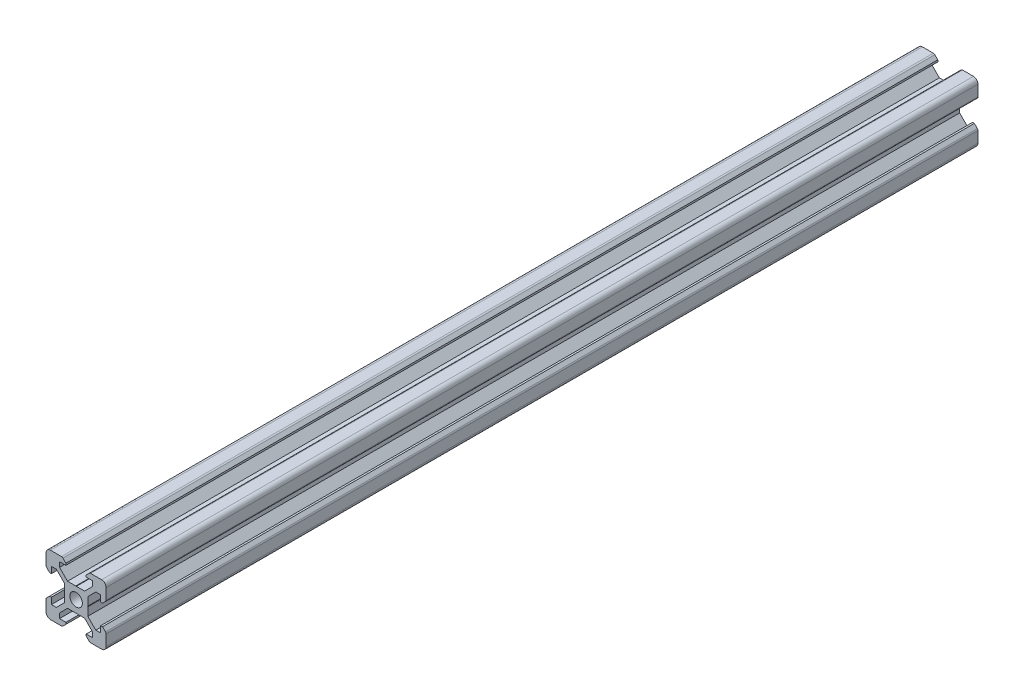
SolidWorks part; units mm, degrees
ref_plane "Front" through (0, 0, 0) normal (0, 0, 1) x (1, 0, 0)
ref_plane "Top" through (0, 0, 0) normal (0, 1, 0) x (1, 0, 0)
ref_plane "Right" through (0, 0, 0) normal (1, 0, 0) x (0, 0, -1)
sketch "Sketch1" plane through (0, 0, 0) normal (0, 0, 1) x (1, 0, 0)
  line L0 (-8.5, 10) -> (-10, 8.5) construction
  line L1 (-8.5, 10) -> (-4.8628, 10)
  line L2 (-10, 8.5) -> (-10, 4.8628)
  line L3 (-8.5, -10) -> (-4.8628, -10)
  line L4 (10, 8.5) -> (10, 4.8628)
  line L5 (-10, 10) -> (10, -10) construction
  line L6 (-10, -10) -> (10, 10) construction
  line L7 (-5.5, -8.2) -> (-3.3865, -8.2)
  line L8 (-8.2, -5.5) -> (-8.2, -3.3865)
  line L9 (-5.5, 8.2) -> (-3.3865, 8.2)
  line L10 (8.2, -5.5) -> (8.2, -3.3865)
  line L11 (-3.9005, 2.8395) -> (-6.561, 5.5)
  line L12 (-6.561, 5.5) -> (-8.2, 5.5)
  line L13 (-2.8395, -3.9005) -> (-0.1, -3.9005)
  line L14 (-3.9005, -2.8395) -> (-3.9005, -0.1)
  line L15 (-2.8395, 3.9005) -> (-0.1, 3.9005)
  line L16 (3.9005, -2.8395) -> (3.9005, -0.1)
  line L17 (-8.2, 3.3865) -> (-8.81, 3.3865)
  line L18 (-8.81, 3.3865) -> (-9.7976, 4.3741)
  line L19 (8.5, 10) -> (10, 8.5) construction
  line L20 (-2.8395, 3.9005) -> (-5.5, 6.561)
  line L21 (-5.5, 6.561) -> (-5.5, 8.2)
  line L22 (-3.3865, 8.2) -> (-3.3865, 8.81)
  line L23 (-3.3865, 8.81) -> (-4.3741, 9.7976)
  line L24 (0, 24.069) -> (0, -33.8154) construction
  line L25 (3.3865, 8.81) -> (4.3741, 9.7976)
  line L26 (3.3865, 8.2) -> (3.3865, 8.81)
  line L27 (5.5, 6.561) -> (5.5, 8.2)
  line L28 (2.8395, 3.9005) -> (5.5, 6.561)
  line L29 (3.3865, 8.2) -> (5.5, 8.2)
  line L30 (4.8628, 10) -> (8.5, 10)
  line L31 (-0.1, 3.9005) -> (0, 3.8005)
  line L32 (0.1, 3.9005) -> (0, 3.8005)
  line L33 (0.1, 3.9005) -> (2.8395, 3.9005)
  line L34 (25.9287, 0) -> (-28.3459, 0) construction
  line L35 (-0.1, -3.9005) -> (0, -3.8005)
  line L36 (0.1, -3.9005) -> (0, -3.8005)
  line L37 (0.1, -3.9005) -> (2.8395, -3.9005)
  line L38 (-3.9005, 0.1) -> (-3.8005, 0)
  line L39 (-3.8005, 0) -> (-3.9005, -0.1)
  line L40 (-3.9005, 0.1) -> (-3.9005, 2.8395)
  line L41 (3.9005, 0.1) -> (3.8005, 0)
  line L42 (3.8005, 0) -> (3.9005, -0.1)
  line L43 (3.9005, 0.1) -> (3.9005, 2.8395)
  line L44 (8.81, 3.3865) -> (9.7976, 4.3741)
  line L45 (8.2, 3.3865) -> (8.81, 3.3865)
  line L46 (6.561, 5.5) -> (8.2, 5.5)
  line L47 (3.9005, 2.8395) -> (6.561, 5.5)
  line L48 (2.8395, -3.9005) -> (5.5, -6.561)
  line L49 (3.9005, -2.8395) -> (6.561, -5.5)
  line L50 (-2.8395, -3.9005) -> (-5.5, -6.561)
  line L51 (-3.9005, -2.8395) -> (-6.561, -5.5)
  line L52 (6.561, -5.5) -> (8.2, -5.5)
  line L53 (-6.561, -5.5) -> (-8.2, -5.5)
  line L54 (-8.81, -3.3865) -> (-9.7976, -4.3741)
  line L55 (-8.2, -3.3865) -> (-8.81, -3.3865)
  line L56 (8.81, -3.3865) -> (9.7976, -4.3741)
  line L57 (8.2, -3.3865) -> (8.81, -3.3865)
  line L58 (8.2, 3.3865) -> (8.2, 5.5)
  line L59 (10, -4.8628) -> (10, -8.5)
  line L60 (-8.2, 3.3865) -> (-8.2, 5.5)
  line L61 (-10, -4.8628) -> (-10, -8.5)
  line L62 (-3.3865, -8.81) -> (-4.3741, -9.7976)
  line L63 (-3.3865, -8.2) -> (-3.3865, -8.81)
  line L64 (3.3865, -8.81) -> (4.3741, -9.7976)
  line L65 (3.3865, -8.2) -> (3.3865, -8.81)
  line L66 (-5.5, -6.561) -> (-5.5, -8.2)
  line L67 (5.5, -6.561) -> (5.5, -8.2)
  line L68 (3.3865, -8.2) -> (5.5, -8.2)
  line L69 (4.8628, -10) -> (8.5, -10)
  circle A0 centre (0, 0) radius 2.1
  arc A1 (-8.5, 10) -> (-10, 8.5) centre (-8.5, 8.5) ccw
  arc A2 (10, 8.5) -> (8.5, 10) centre (8.5, 8.5) ccw
  arc A3 (-4.3741, 9.7976) -> (-4.8628, 10) centre (-4.8628, 9.3088) ccw
  arc A4 (4.8628, 10) -> (4.3741, 9.7976) centre (4.8628, 9.3088) ccw
  arc A5 (-8.5, -10) -> (-10, -8.5) centre (-8.5, -8.5) cw
  arc A6 (9.7976, 4.3741) -> (10, 4.8628) centre (9.3088, 4.8628) ccw
  arc A7 (-10, 4.8628) -> (-9.7976, 4.3741) centre (-9.3088, 4.8628) ccw
  arc A8 (-10, -4.8628) -> (-9.7976, -4.3741) centre (-9.3088, -4.8628) cw
  arc A9 (9.7976, -4.3741) -> (10, -4.8628) centre (9.3088, -4.8628) cw
  arc A10 (10, -8.5) -> (8.5, -10) centre (8.5, -8.5) cw
  arc A11 (-4.3741, -9.7976) -> (-4.8628, -10) centre (-4.8628, -9.3088) cw
  arc A12 (4.8628, -10) -> (4.3741, -9.7976) centre (4.8628, -9.3088) cw
  point P17 (-9.25, 9.25)
  point P21 (9.25, 9.25)
  dimension "D2" = 4.2
  dimension "D4" = 1.5
  dimension "D3" = 20
  dimension "D5" = 0.529
  dimension "D6" = 6.773
  dimension "D7" = 90
  dimension "D8" = 11
  dimension "D9" = 0.61
  dimension "D10" = 0.1
  dimension "D11" = 0.1
  dimension "D12" = 0.1
  dimension "D13" = 0.1
  dimension "D14" = 5.679
  dimension "D15" = 1.639
  dimension "D16" = 1.8
  dimension "D17" = 90
  dimension "D18" = 6.773
  dimension "D19" = 90
extrude "Boss-Extrude1" add sketch "Sketch1" along normal blind 290
